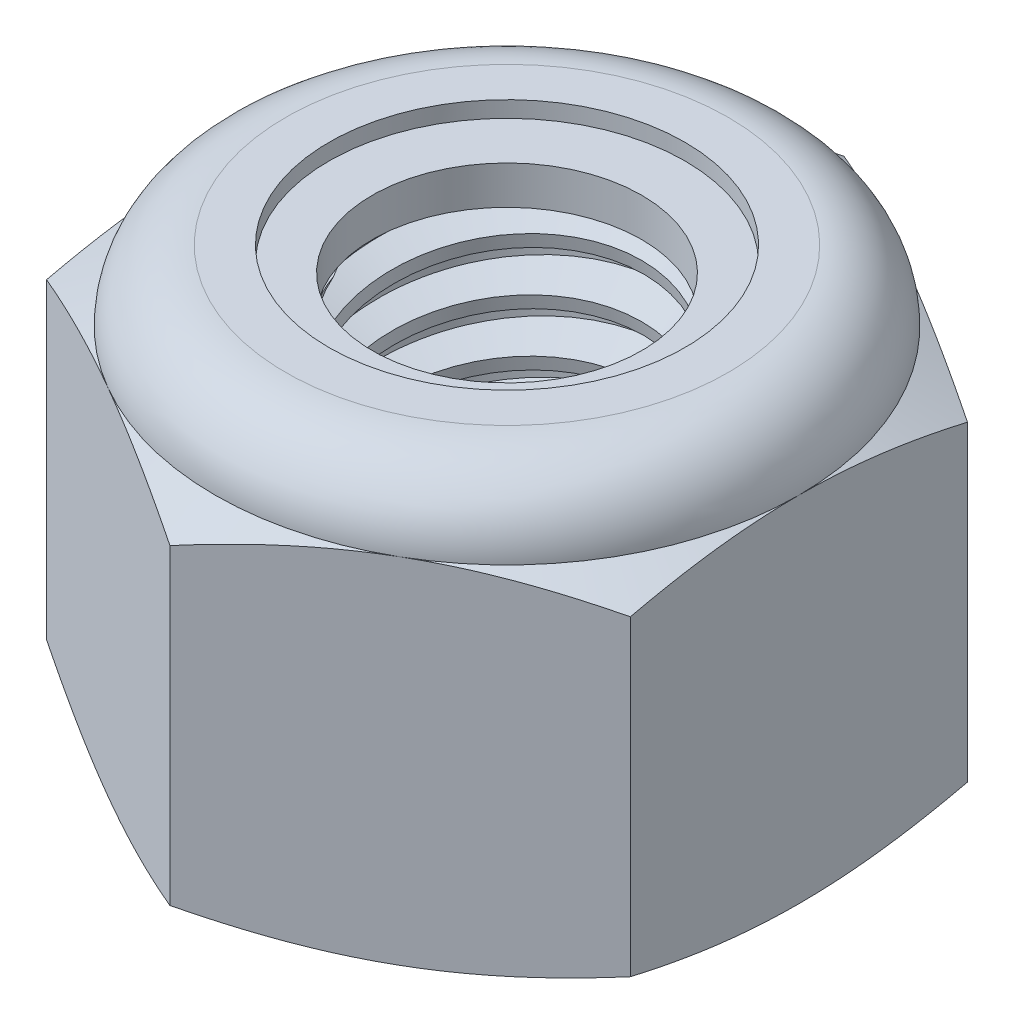
SolidWorks part; units mm, degrees
ref_plane "Front" through (0, 0, 0) normal (0, 0, 1) x (1, 0, 0)
ref_plane "Top" through (0, 0, 0) normal (0, 1, 0) x (1, 0, 0)
ref_plane "Right" through (0, 0, 0) normal (1, 0, 0) x (0, 0, -1)
sketch "Sketch1" plane through (0, 0, 0) normal (0, 1, 0) x (1, 0, 0)
  line L1 (0, 3.1754) -> (-2.75, 1.5877)
  line L2 (-2.75, 1.5877) -> (-2.75, -1.5877)
  line L3 (-2.75, -1.5877) -> (0, -3.1754)
  line L4 (0, -3.1754) -> (2.75, -1.5877)
  line L5 (2.75, -1.5877) -> (2.75, 1.5877)
  line L6 (2.75, 1.5877) -> (0, 3.1754)
  circle A0 centre (0, 0) radius 2.75 construction
  dimension "Hex Flats" = 5.5
extrude "Extrude1" add sketch "Sketch1" along normal blind 4
sketch "Sketch2" plane through (0, 0, 0) normal (1, 0, 0) x (0, 0, -1)
  line L0 (-1.5, 0) -> (-1.5, 4) construction
  line L1 (0, 0) -> (1.5, 0)
  line L2 (0, 0) -> (0, 4)
  line L3 (0, 4) -> (1.5, 4)
  line L4 (1.5, 0) -> (1.5, 4)
  line L5 (-1.5877, 4) -> (1.5877, 4) construction
  line L7 (0, -1.5) -> (0, 0) construction
  dimension "Thread Dia" = 3
revolve "Revolve1" add sketch "Sketch2" angle 360 about L7
sketch "Sketch3" plane through (0, 0, 0) normal (1, 0, 0) x (0, 0, -1)
  line L0 (1.5, 4) -> (-1.5, 4) construction
  line L1 (-1.5, 4) -> (-1.5, 3.5) construction
  line L2 (-1.5, 3.5) -> (1.5, 4) construction
  line L3 (1.5, 4) -> (1.5103, 3.9384) construction
  line L4 (1.5103, 3.9384) -> (1.5822, 3.5068)
  line L5 (1.5822, 3.5068) -> (1.2896, 3.6164)
  line L6 (1.2896, 3.6164) -> (1.269, 3.7397)
  line L7 (1.269, 3.7397) -> (1.5103, 3.9384)
  line L8 (1.2793, 3.6781) -> (1.5462, 3.7226) construction
  line L9 (1.5, 4) -> (1.5, 3.7149) construction
  line L10 (1.5, 3.7149) -> (-1.5, 3.2149) construction
  line L11 (-1.5, 3.2149) -> (-1.5, 3.5) construction
  line L12 (-0.0892, 4) -> (0.0892, 2.9297) construction
  line L13 (-1.5, 0) -> (-1.5, 4) construction
  line L14 (0, 4) -> (1.5, 4) construction
  line L15 (1.5, 0) -> (1.5, 4) construction
  point P13 (0, 3.4649)
  dimension "D1" = 0.0625
  dimension "D2" = 0.125
  dimension "Thread Pitch" = 0.5
  dimension "D4" = 60
  dimension "D5" = 0.5
revolve "Cut-Revolve1" cut sketch "Sketch3" angle 360 about L12
pattern_linear "LPattern1" count 8 spacing 0.5 along (0, -1, 0) count 2 spacing 0.5 along (0, 1, 0) of "Cut-Revolve1"
sketch "Sketch4" plane through (0, 0, 0) normal (1, 0, 0) x (0, 0, -1)
  line L0 (0, 4) -> (1.5, 4)
  line L1 (1.5, 4) -> (1.269, 3.8923)
  line L2 (1.269, 3.8923) -> (1.269, 0.1077)
  line L3 (1.269, 0.1077) -> (1.5, 0)
  line L4 (1.5, 0) -> (0, 0)
  line L5 (0, 0) -> (0, 4)
  line L6 (1.5, 0) -> (1.5, 4) construction
  line L7 (0, 4) -> (1.5, 4) construction
  line L8 (0, 0) -> (1.5, 0) construction
  line L9 (0, 0) -> (0, 4) construction
  line L10 (0, 4) -> (0, 4.2549) construction
  dimension "D1" = 25
revolve "Cut-Revolve2" cut sketch "Sketch4" angle 360 about L10
combine bodies "Combine1" operation type subtract main body 112 bodies to subtract 111
sketch "Sketch5" plane through (0, 0, 0) normal (1, 0, 0) x (0, 0, -1)
  line L0 (0, 0) -> (2.75, 0)
  line L1 (2.75, 0) -> (3.1754, 0.1984)
  line L2 (3.1754, 0.1984) -> (3.1754, 3.135)
  line L3 (3.1754, 3.135) -> (2.75, 3.3333)
  line L4 (2.0833, 4) -> (2.0833, 5.27)
  line L5 (2.0833, 5.27) -> (4.4454, 5.27)
  line L6 (4.4454, 5.27) -> (4.4454, -1.27)
  line L7 (4.4454, -1.27) -> (0, -1.27)
  line L8 (0, -1.27) -> (0, 0)
  line L9 (2.75, 3.3333) -> (2.75, 0) construction
  line L10 (0, 0) -> (1.5, 0) construction
  line L13 (3.1754, 1.6667) -> (4.4454, 1.6667) construction
  line L14 (3.1754, 4) -> (3.1754, 0) construction
  line L15 (0, 0) -> (0, 5.27) construction
  line L20 (0, 5.27) -> (2.0833, 5.27) construction
  line L22 (0, 4) -> (1.5, 4) construction
  arc A0 (2.75, 3.3333) -> (2.0833, 4) centre (2.0833, 3.3333) ccw
  dimension "D1" = 25
  dimension "D2" = 1.27
  dimension "D3" = 4
  dimension "D4" = 0.6667
revolve "Cut-Revolve3" cut sketch "Sketch5" angle 360 about L15
sketch "Sketch6" plane through (0, 0, 0) normal (1, 0, 0) x (0, 0, -1)
  line L0 (0, 3.3333) -> (2.5976, 3.3333)
  line L1 (2.0833, 3.8476) -> (1.6762, 3.8476)
  line L2 (0, 5.27) -> (0, 3.3333)
  line L3 (1.6762, 5.27) -> (0, 5.27)
  line L4 (0, 5.27) -> (2.0833, 5.27) construction
  line L5 (0, 0) -> (0, 5.27) construction
  line L6 (0, 5.27) -> (0, 44.323) construction
  line L7 (1.6762, 3.8476) -> (1.6762, 5.27)
  line L8 (2.0833, 4) -> (2.0833, 3.8476) construction
  line L9 (1.6762, 3.8476) -> (1.269, 3.8476) construction
  line L10 (1.269, 3.8476) -> (1.269, 3.8923) construction
  arc A0 (2.5976, 3.3333) -> (2.0833, 3.8476) centre (2.0833, 3.3333) ccw
  arc A1 (2.75, 3.3333) -> (2.0833, 4) centre (2.0833, 3.3333) ccw construction
  dimension "D1" = 0.1524
revolve "Cut-Revolve4" cut sketch "Sketch6" angle 360 about L6
sketch "Sketch7" plane through (0, 0, 0) normal (1, 0, 0) x (0, 0, -1)
  line L0 (1.269, 3.4095) -> (2.5147, 3.4095)
  line L1 (2.0833, 3.7714) -> (1.269, 3.7714)
  line L2 (1.269, 3.7714) -> (1.269, 3.4095)
  line L3 (1.269, 3.4095) -> (0, 3.4095) construction
  line L4 (0, 3.4095) -> (0, 3.7714) construction
  line L5 (0, 3.7714) -> (1.269, 3.7714) construction
  line L6 (1.269, 3.4095) -> (1.269, 3.3333) construction
  line L7 (0, 3.3333) -> (2.5976, 3.3333) construction
  line L8 (2.0833, 3.7714) -> (2.0833, 3.8476) construction
  arc A0 (2.5147, 3.4095) -> (2.0833, 3.7714) centre (2.0833, 3.3333) ccw
  arc A2 (2.5976, 3.3333) -> (2.0833, 3.8476) centre (2.0833, 3.3333) ccw construction
  dimension "D1" = 0.0762
revolve "Revolve2" add sketch "Sketch7" angle 360 about L4
equation "\"D1@Sketch3\"=\"Thread Pitch@Sketch3\"/8"
equation "\"D2@Sketch3\"=\"Thread Pitch@Sketch3\"/4"
equation "\"D5@Sketch3\"=\"Thread Pitch@Sketch3\""
equation "\"D4@LPattern1\"=\"Thread Pitch@Sketch3\""
equation "\"D3@LPattern1\"=\"Thread Pitch@Sketch3\""
equation "\"D1@LPattern1\"=\"Height@Extrude1\"/\"Thread Pitch@Sketch3\""
equation "\"D4@Sketch5\"=\"Height@Extrude1\"/6"
